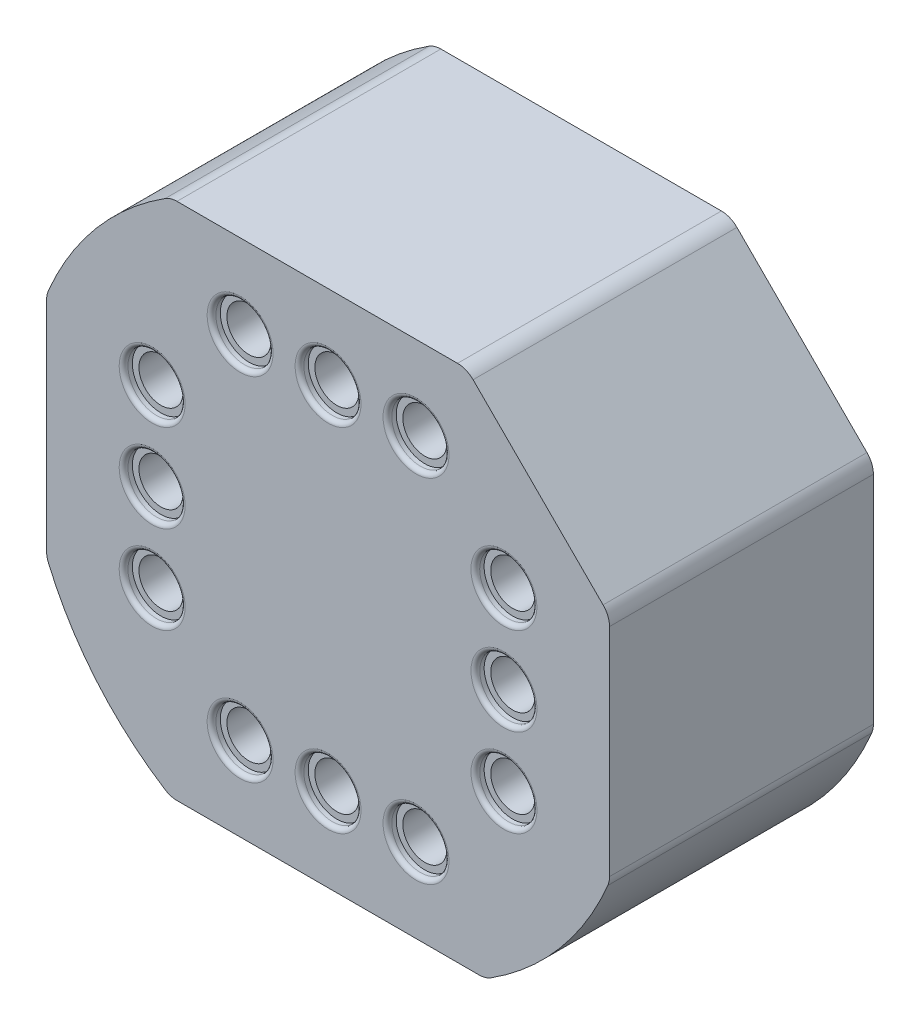
SolidWorks part; units mm, degrees
ref_plane "Front" through (0, 0, 0) normal (0, 0, 1) x (1, 0, 0)
ref_plane "Top" through (0, 0, 0) normal (0, 1, 0) x (1, 0, 0)
ref_plane "Right" through (0, 0, 0) normal (1, 0, 0) x (0, 0, -1)
sketch "Sketch1" plane through (0, 0, 0) normal (0, 0, 1) x (1, 0, 0)
  line L0 (4.0017, 7.493) -> (8.128, 3.3667)
  line L1 (-4.5437, -7.493) -> (4.5437, -7.493)
  line L2 (-8.128, -3.275) -> (-8.128, 3.275)
  line L3 (-4.5437, 7.493) -> (4.0017, 7.493)
  line L4 (8.128, -3.275) -> (8.128, 3.3667)
  circle A0 centre (0, 5.08) radius 0.635
  circle A1 centre (-5.08, 2.54) radius 0.635
  circle A2 centre (5.08, 2.54) radius 0.635
  arc A3 (-8.128, 3.275) -> (-4.5437, 7.493) centre (0, 0) cw
  arc A4 (8.128, -3.275) -> (4.5437, -7.493) centre (0, 0) cw
  arc A5 (-4.5437, -7.493) -> (-8.128, -3.275) centre (0, 0) cw
  circle A6 centre (-2.54, 5.08) radius 0.635
  circle A7 centre (2.54, 5.08) radius 0.635
  circle A8 centre (-5.08, 0) radius 0.635
  circle A9 centre (-5.08, -2.54) radius 0.635
  circle A10 centre (-2.54, -5.08) radius 0.635
  circle A11 centre (0, -5.08) radius 0.635
  circle A12 centre (2.54, -5.08) radius 0.635
  circle A13 centre (5.08, -2.54) radius 0.635
  circle A14 centre (5.08, 0) radius 0.635
  point P0 (0, 0)
  dimension "D3" = 1.27
  dimension "D4" = 1.27
  dimension "D5" = 1.27
  dimension "D11" = 5.08
  dimension "D14" = 225
  dimension "D16" = 1.27
  dimension "D17" = 1.27
  dimension "D18" = 1.27
  dimension "D19" = 1.27
  dimension "D20" = 1.27
  dimension "D21" = 1.27
  dimension "D22" = 1.27
  dimension "D23" = 1.27
  dimension "D24" = 1.27
  dimension "D25" = 2.54
  dimension "D2" = 7.493
  dimension "D6" = 2.54
  dimension "D7" = 5.08
  dimension "D8" = 5.08
  dimension "D9" = 7.493
  dimension "D10" = 2.54
  dimension "D12" = 8.128
  dimension "D13" = 8.128
  dimension "D15" = 8.128
  dimension "D26" = 2.54
  dimension "D27" = 5.08
  dimension "D28" = 5.08
  dimension "D29" = 2.54
  dimension "D30" = 5.08
  dimension "D31" = 5.08
  dimension "D32" = 2.54
  dimension "D33" = 2.54
  dimension "D34" = 2.54
  dimension "D35" = 5.08
  dimension "D36" = 5.08
  dimension "D37" = 2.54
  dimension "D38" = 2.54
  dimension "D39" = 2.54
extrude "Boss-Extrude1" add sketch "Sketch1" along normal blind 7.62
fillet "Fillet1" radius 0.635 8 edges at (8.128, 3.3667, 3.81) (4.5437, -7.493, 3.81) (-4.5437, -7.493, 3.81) (-8.128, -3.275, 3.81) (-4.5437, 7.493, 3.81) (4.0017, 7.493, 3.81) (8.128, -3.275, 3.81) (-8.128, 3.275, 3.81)
sketch "Sketch2" plane through (0, 0, 7.62) normal (0, 0, 1) x (1, 0, 0)
  circle A0 centre (0, 5.08) radius 0.8255
  circle A1 centre (5.08, -2.54) radius 0.8255
  circle A2 centre (-2.54, 5.08) radius 0.8255
  circle A3 centre (-5.08, 2.54) radius 0.8255
  circle A4 centre (-5.08, 0) radius 0.8255
  circle A5 centre (-5.08, -2.54) radius 0.8255
  circle A6 centre (-2.54, -5.08) radius 0.8255
  circle A7 centre (0, -5.08) radius 0.8255
  circle A8 centre (2.54, -5.08) radius 0.8255
  circle A9 centre (5.08, 0) radius 0.8255
  circle A10 centre (5.0774, 2.5387) radius 0.8255
  circle A11 centre (2.54, 5.08) radius 0.8255
  dimension "D1" = 1.651
  dimension "D2" = 1.651
  dimension "D3" = 1.651
  dimension "D24" = 1.651
  dimension "D25" = 1.651
  dimension "D26" = 1.651
  dimension "D27" = 1.651
  dimension "D28" = 1.651
  dimension "D29" = 1.651
  dimension "D30" = 1.651
  dimension "D31" = 1.651
  dimension "D32" = 1.651
  dimension "D4" = 2.54
  dimension "D5" = 5.08
  dimension "D6" = 5.08
  dimension "D8" = 5.08
  dimension "D9" = 5.08
  dimension "D10" = 5.08
  dimension "D11" = 5.08
  dimension "D12" = 2.54
  dimension "D13" = 2.54
  dimension "D14" = 2.54
  dimension "D15" = 2.54
  dimension "D16" = 5.08
  dimension "D18" = 5.08
  dimension "D19" = 5.08
  dimension "D20" = 2.54
  dimension "D21" = 2.54
  dimension "D22" = 5.08
  dimension "D23" = 5.08
extrude "Cut-Extrude1" cut sketch "Sketch2" against normal blind 0.254 contours A2 | A1 | A0 | A11 | A10 | A9 | A8 | A7 | A6 | A5 | A4 | A3
fillet "Fillet3" radius 0.127 12 edges at (5.9055, -2.54, 7.62) (-1.7145, 5.08, 7.62) (0.8255, 5.08, 7.62) (-4.2545, -2.54, 7.62) (-1.7145, -5.08, 7.62) (0.8255, -5.08, 7.62) (3.3655, -5.08, 7.62) (5.9055, 0, 7.62) (5.9029, 2.5387, 7.62) (3.3655, 5.08, 7.62) (-4.2545, 2.54, 7.62) (-4.2545, 0, 7.62)
chamfer "Chamfer1" distance 0.3302 angle 45 12 edges at (-4.445, 2.54, 0) (5.715, 2.54, 0) (0.635, 5.08, 0) (5.715, 0, 0) (5.715, -2.54, 0) (3.175, -5.08, 0) (0.635, -5.08, 0) (-1.905, -5.08, 0) (-4.445, -2.54, 0) (-4.445, 0, 0) (-1.905, 5.08, 0) (3.175, 5.08, 0)
fillet "Fillet5" radius 0.254 12 edges at (-5.715, 2.54, 0.3302) (4.445, 2.54, 0.3302) (-0.635, 5.08, 0.3302) (4.445, 0, 0.3302) (4.445, -2.54, 0.3302) (1.905, -5.08, 0.3302) (-0.635, -5.08, 0.3302) (-3.175, -5.08, 0.3302) (-5.715, -2.54, 0.3302) (-5.715, 0, 0.3302) (-3.175, 5.08, 0.3302) (1.905, 5.08, 0.3302)
